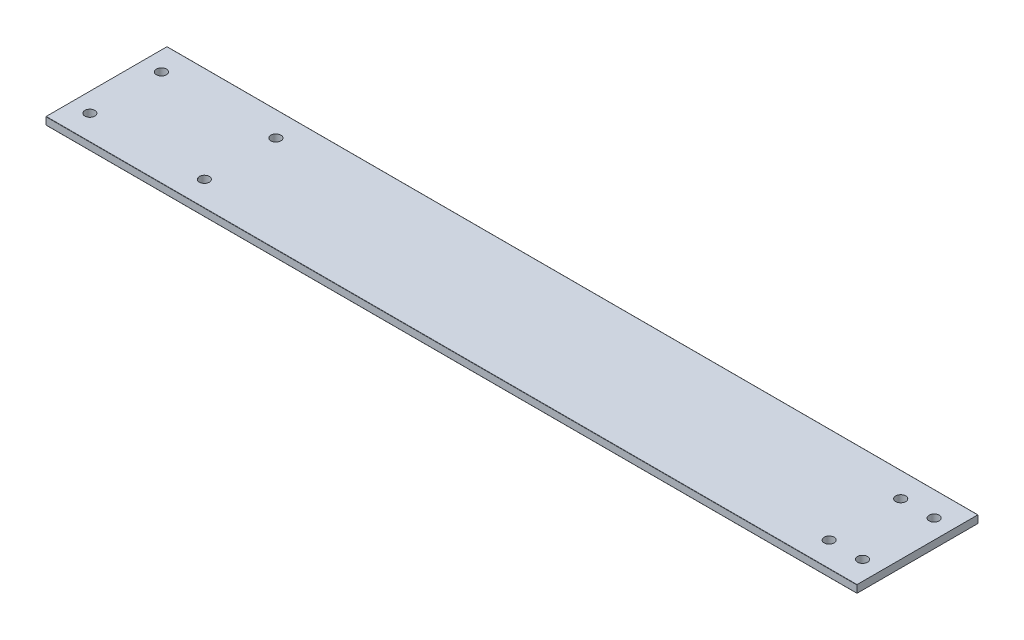
SolidWorks part; units mm, degrees
ref_plane "Front Plane" through (0, 0, 0) normal (0, 0, 1) x (1, 0, 0)
ref_plane "Top Plane" through (0, 0, 0) normal (0, 1, 0) x (1, 0, 0)
ref_plane "Right Plane" through (0, 0, 0) normal (1, 0, 0) x (0, 0, -1)
sketch "Sketch1" plane through (0, 0, 0) normal (0, 1, 0) x (1, 0, 0)
  line L1 (304.8, -25.4) -> (-304.8, -25.4)
  line L2 (304.8, -25.4) -> (304.8, 25.4)
  line L3 (304.8, 25.4) -> (-304.8, 25.4)
  line L4 (-304.8, -25.4) -> (-304.8, 25.4)
  line L5 (304.8, -25.4) -> (-304.8, 25.4) construction
  line L6 (304.8, 25.4) -> (-304.8, -25.4) construction
  point P0 (0, 0)
  dimension "Length" = 609.6
  dimension "Width" = 50.8
sketch "Sketch2" plane through (0, 0, 0) normal (1, 0, 0) x (0, 0, -1)
  line L0 (25.4, 1.5875) -> (25.4, -1.5875) construction
  point P2 (25.4, 0)
  dimension "Thickness" = 3.175
sketch "Sketch3" plane through (0, 0, 0) normal (0, 1, 0) x (1, 0, 0)
  line L1 (-304.8, 25.4) -> (304.8, 25.4)
  line L2 (-304.8, 25.4) -> (-304.8, -25.4)
  line L3 (-304.8, -25.4) -> (304.8, -25.4)
  line L4 (304.8, 25.4) -> (304.8, -25.4)
extrude "Boss-Extrude1" add sketch "Sketch3" against normal up to vertex (1.5875 mm away) and the other way up to vertex (1.5875 mm away) up to point (0, -1.5875, -25.4) other way up to point (0, 1.5875, -25.4)
fillet "Fillet1" radius 0.1048 4 edges at (0, -1.5875, 25.4) (0, -1.5875, -25.4) (0, 1.5875, -25.4) (0, 1.5875, 25.4)
sketch "Sketch4" plane through (304.8, 0, 0) normal (1, 0, 0) x (0, 0, -1)
  line L0 (-25.4, -1.4827) -> (-25.4, 1.4827) construction
  line L1 (-25.4, -1.5875) -> (25.4, -1.5875)
  line L2 (-25.4, -1.5875) -> (-25.4, 1.5875)
  line L3 (-25.4, 1.5875) -> (25.4, 1.5875)
  line L4 (25.4, -1.5875) -> (25.4, 1.5875)
extrude "Cut-Extrude1" cut sketch "Sketch4" against normal up to surface (269.6 mm away)
sketch "Sketch5" plane through (0, -1.5875, 0) normal (0, -1, 0) x (1, 0, 0)
  line L1 (-296.8, 15) -> (-248.8, 15) construction
  line L2 (-296.8, 15) -> (-296.8, -15) construction
  line L3 (-296.8, -15) -> (-248.8, -15) construction
  line L4 (-248.8, 15) -> (-248.8, -15) construction
  line L5 (27.2, 15) -> (13.199, 15) construction
  line L6 (27.2, 15) -> (27.2, -15) construction
  line L7 (27.2, -15) -> (13.199, -15) construction
  line L8 (13.199, 15) -> (13.199, -15) construction
  circle A0 centre (27.2, -15) radius 2.1
  circle A1 centre (27.2, 15) radius 2.1
  circle A2 centre (13.199, 15) radius 2.1
  circle A3 centre (13.199, -15) radius 2.1
  circle A4 centre (-248.8, -15) radius 2.1
  circle A5 centre (-248.8, 15) radius 2.1
  circle A6 centre (-296.8, 15) radius 2.1
  circle A7 centre (-296.8, -15) radius 2.1
  circle A8 centre (27.2, -15) radius 2.15 construction
  circle A9 centre (13.199, 15) radius 2.15 construction
  circle A10 centre (-296.8, -15) radius 2.15 construction
  circle A11 centre (-248.8, 15) radius 2.15 construction
  dimension "D1" = 4.2
extrude "Cut-Extrude2" cut sketch "Sketch5" against normal through all
equation "\"D1@Fillet1\" = \"Thickness@Sketch2\" * .033"
equation "\"!\"=0.1"
